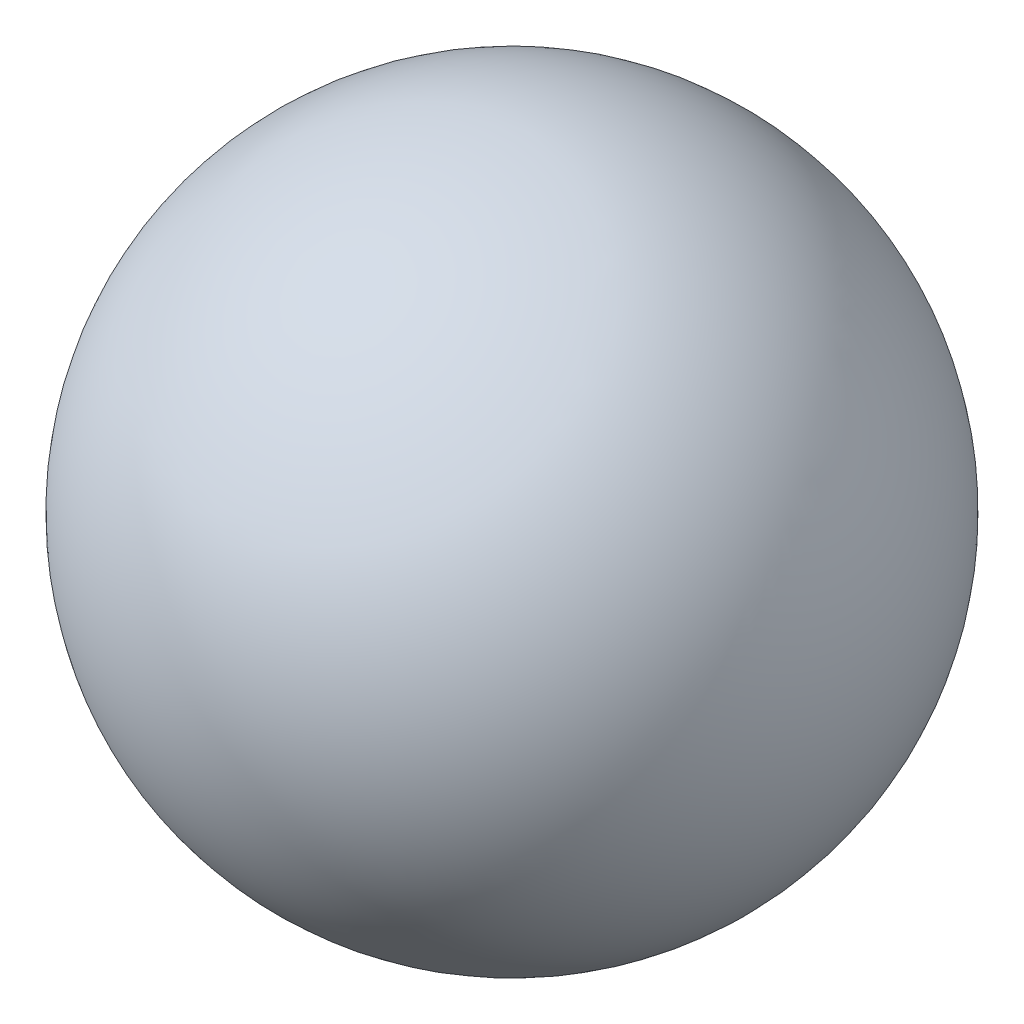
SolidWorks part; units mm, degrees
material "Rubber"
ref_plane "Front Plane" through (0, 0, 0) normal (0, 0, 1) x (1, 0, 0)
ref_plane "Top Plane" through (0, 0, 0) normal (0, 1, 0) x (1, 0, 0)
ref_plane "Right Plane" through (0, 0, 0) normal (1, 0, 0) x (0, 0, -1)
sketch "Sketch3" plane through (0, 0, 0) normal (0, 0, 1) x (1, 0, 0)
  line L0 (52.523, 55.2067) -> (-52.523, -55.2067)
  arc A0 (-52.523, -55.2067) -> (52.523, 55.2067) centre (0, 0) ccw
revolve "Revolve1" add sketch "Sketch3" angle 360 about L0
